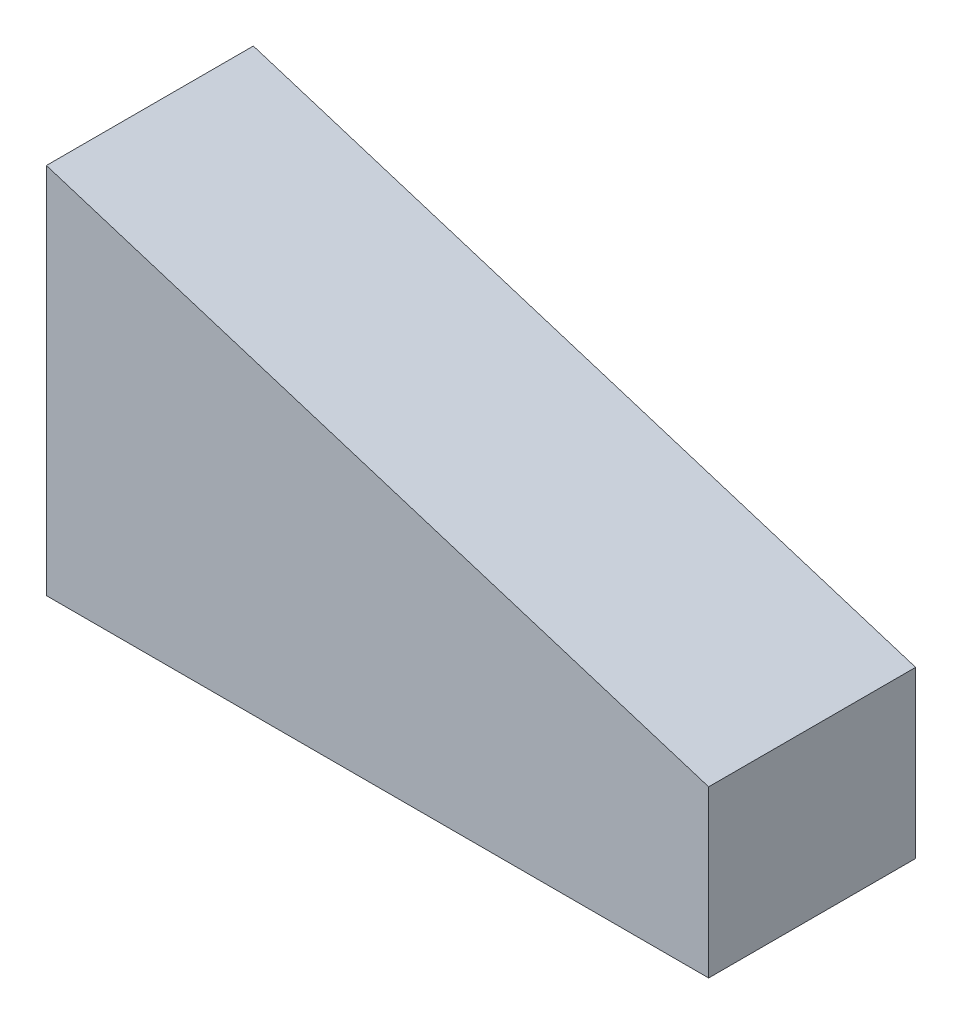
SolidWorks part; units mm, degrees
ref_plane "Front Plane" through (0, 0, 0) normal (0, 0, 1) x (1, 0, 0)
ref_plane "Top Plane" through (0, 0, 0) normal (0, 1, 0) x (1, 0, 0)
ref_plane "Right Plane" through (0, 0, 0) normal (1, 0, 0) x (0, 0, -1)
sketch "Sketch1" plane through (0, 0, 0) normal (0, 0, 1) x (1, 0, 0)
  line L0 (0, 0) -> (80, 0)
  line L1 (80, 0) -> (80, 20)
  line L2 (80, 20) -> (0, 45)
  line L3 (0, 45) -> (0, 0)
  dimension "D1" = 45
  dimension "D2" = 80
  dimension "D3" = 20
extrude "Boss-Extrude2" add sketch "Sketch1" along normal blind 25
